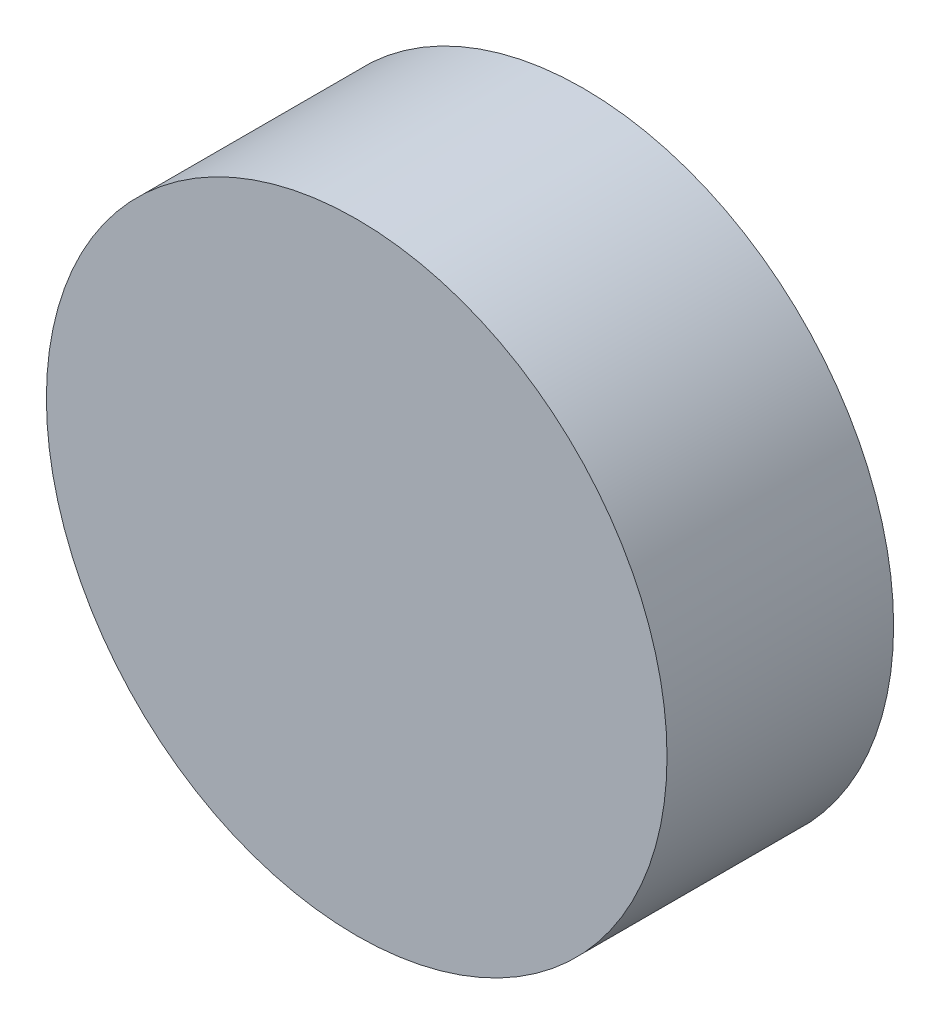
SolidWorks part; units mm, degrees
ref_plane "前视基准面" through (0, 0, 0) normal (0, 0, 1) x (1, 0, 0)
ref_plane "上视基准面" through (0, 0, 0) normal (0, 1, 0) x (1, 0, 0)
ref_plane "右视基准面" through (0, 0, 0) normal (1, 0, 0) x (0, 0, -1)
sketch "草图1" plane through (0, 0, 0) normal (0, 0, 1) x (1, 0, 0)
  circle A0 centre (20.2496, 12.3126) radius 3.15
extrude "凸台-拉伸1" add sketch "草图1" along normal blind 2.3
